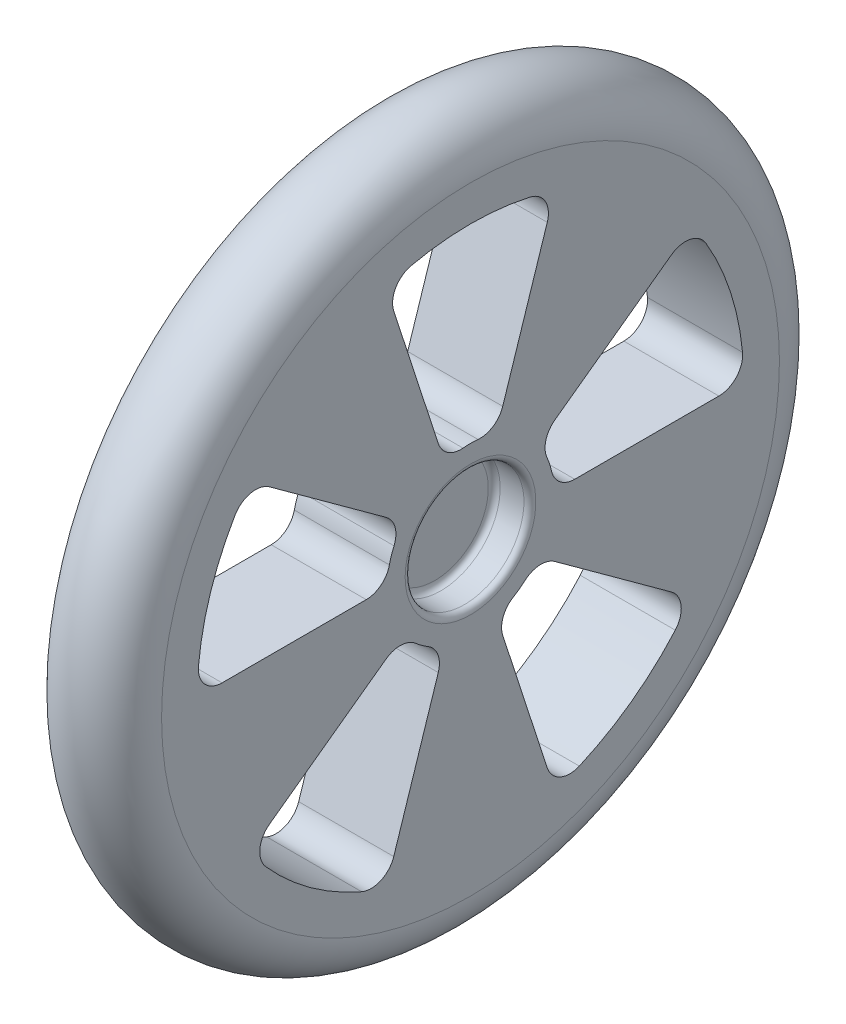
SolidWorks part; units mm, degrees
ref_plane "Front Plane" through (0, 0, 0) normal (0, 0, 1) x (1, 0, 0)
ref_plane "Top Plane" through (0, 0, 0) normal (0, 1, 0) x (1, 0, 0)
ref_plane "Right Plane" through (0, 0, 0) normal (1, 0, 0) x (0, 0, -1)
sketch "Sketch3" plane through (0, 0, 0) normal (0, 0, 1) x (1, 0, 0)
  line L0 (0, 0) -> (10.5995, 0) construction
  line L1 (0, 0) -> (0, 26) construction
  line L2 (-1, 0) -> (1, 0)
  line L3 (1, 0) -> (1, 4.5)
  line L4 (1.5, 5) -> (3.5, 5)
  line L5 (4, 5.5) -> (4, 26)
  line L6 (-4, 5.5) -> (-4, 26)
  line L7 (-1.5, 5) -> (-3.5, 5)
  line L8 (-1, 0) -> (-1, 4.5)
  arc A0 (1, 4.5) -> (1.5, 5) centre (1.5, 4.5) cw
  arc A1 (3.5, 5) -> (4, 5.5) centre (3.5, 5.5) ccw
  arc A4 (-3.5, 5) -> (-4, 5.5) centre (-3.5, 5.5) cw
  arc A5 (-1, 4.5) -> (-1.5, 5) centre (-1.5, 4.5) ccw
  arc A6 (4, 26) -> (-4, 26) centre (0, 26) ccw
  point P3 (-1, 0)
  point P4 (0, 30)
  point P12 (1, 5)
  point P15 (4, 5)
  point P18 (1, 0)
  point P29 (0, 0)
  point P30 (-4, 5)
  point P31 (-1, 5)
  dimension "D6" = 0.5
  dimension "D1" = 1
  dimension "D2" = 0
  dimension "D3" = 30
  dimension "D4" = 4
  dimension "D5" = 5
revolve "Revolve1" add sketch "Sketch3" angle 360 about L0
sketch "Sketch6" plane through (4, 0, 0) normal (1, 0, 0) x (0, 0, -1)
  line L0 (7.0991, 5.1578) -> (16.9121, 12.2874)
  line L1 (20.9045, 0) -> (8.775, 0)
  line L2 (0, 0) -> (19.5288, 0) construction
  line L3 (0, 0) -> (0, 5.2799) construction
  line L4 (23, 0) -> (0, 0) construction
  line L5 (18.6074, 13.5191) -> (0, 0) construction
  circle A0 centre (0, 0) radius 5.5 construction
  arc A2 (6.4359, 2.7531) -> (6.825, 1.5556) centre (0, 0) cw
  arc A3 (19.8103, 11.6855) -> (22.8955, 2.1905) centre (0, 0) cw
  circle A4 centre (0, 0) radius 26 construction
  arc A5 (8.775, 0) -> (6.825, 1.5556) centre (8.775, 2) cw
  arc A6 (7.0991, 5.1578) -> (6.4359, 2.7531) centre (8.2747, 3.5398) ccw
  arc A7 (20.9045, 0) -> (22.8955, 2.1905) centre (20.9045, 2) ccw
  arc A8 (16.9121, 12.2874) -> (19.8103, 11.6855) centre (18.0877, 10.6693) cw
  dimension "D1" = 36
  dimension "D3" = 1.5
  dimension "D4" = 3
  dimension "D2" = 2
extrude "Cut-Extrude1" cut sketch "Sketch6" against normal up to next (8 mm away)
pattern_circular "CirPattern1" count 5 over 360 about axis through (0, 0, 0) along (1, 0, 0) of "Cut-Extrude1"
